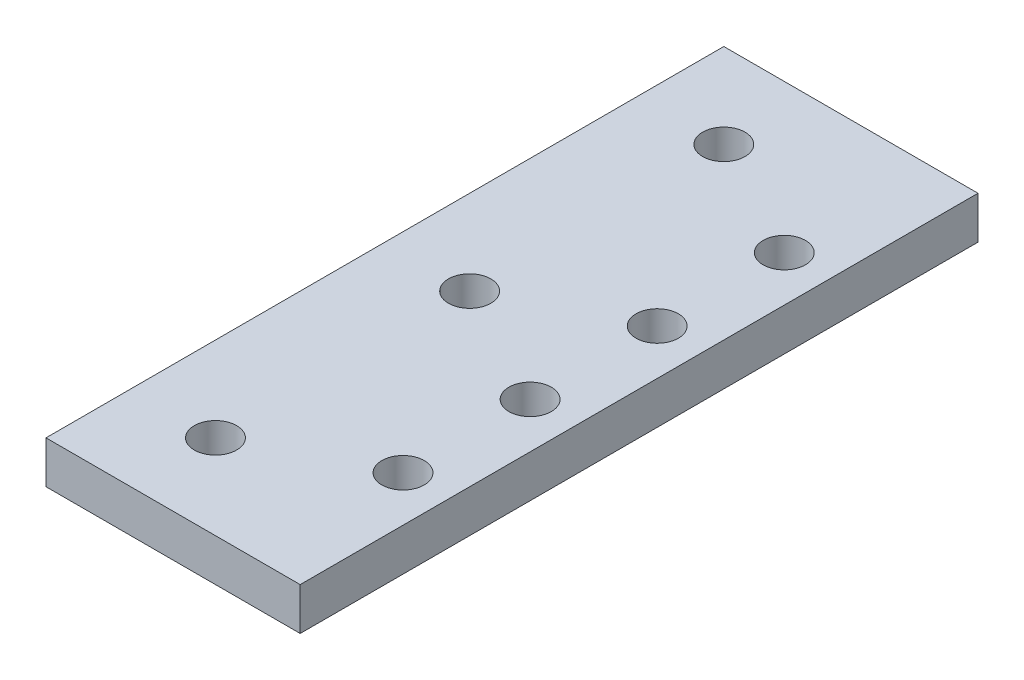
SolidWorks part; units mm, degrees
ref_plane "Front Plane" through (0, 0, 0) normal (0, 0, 1) x (1, 0, 0)
ref_plane "Top Plane" through (0, 0, 0) normal (0, 1, 0) x (1, 0, 0)
ref_plane "Right Plane" through (0, 0, 0) normal (1, 0, 0) x (0, 0, -1)
sketch "Sketch2" plane through (0, 0, 0) normal (0, 1, 0) x (1, 0, 0)
  line L1 (-12.7, -50.8) -> (25.4, -50.8)
  line L2 (-12.7, -50.8) -> (-12.7, 50.8)
  line L3 (-12.7, 50.8) -> (25.4, 50.8)
  line L4 (25.4, -50.8) -> (25.4, 50.8)
  circle A0 centre (0, 0) radius 3.175
  circle A1 centre (0, 38.1) radius 3.175
  circle A2 centre (0, -38.1) radius 3.175
  dimension "D5" = 6.35
  dimension "D6" = 6.35
  dimension "D7" = 38.1
  dimension "D8" = 6.35
  dimension "D9" = 38.1
  dimension "D1" = 50.8
  dimension "D2" = 101.6
  dimension "D3" = 25.4
  dimension "D4" = 12.7
extrude "Boss-Extrude1" add sketch "Sketch2" along normal blind 6.35
sketch "Sketch3" plane through (0, 6.35, 0) normal (0, 1, 0) x (1, 0, 0)
  line L0 (18.5896, -50.8) -> (18.5896, 50.8)
  line L1 (-12.7, -50.8) -> (25.4, -50.8) construction
  line L2 (25.4, 50.8) -> (-12.7, 50.8) construction
  line L3 (25.4, -50.8) -> (25.4, 50.8) construction
  circle A0 centre (18.5896, 28.575) radius 3.175
  circle A1 centre (18.5896, 9.525) radius 3.175
  circle A2 centre (18.5896, -9.525) radius 3.175
  circle A3 centre (18.5896, -28.575) radius 3.175
  dimension "D1" = 6.35
  dimension "D2" = 22.225
  dimension "D4" = 6.8104
  dimension "D3" = 4
extrude "Cut-Extrude2" cut sketch "Sketch3" against normal through all contours A0 | A1 | A2 | A3
